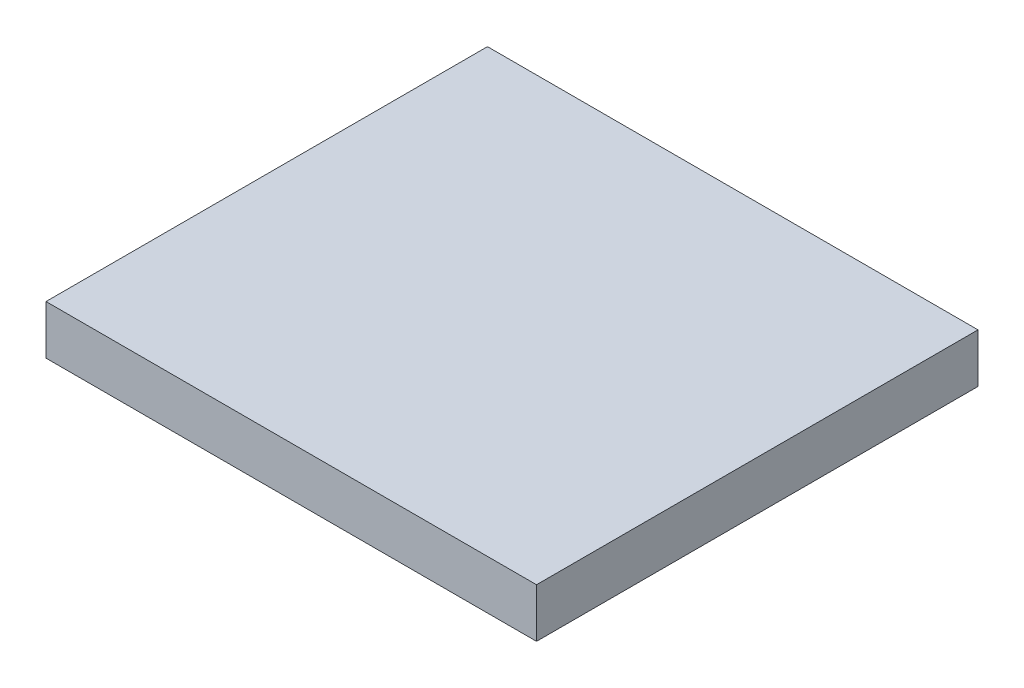
SolidWorks part; units mm, degrees
ref_plane "Front Plane" through (0, 0, 0) normal (0, 0, 1) x (1, 0, 0)
ref_plane "Top Plane" through (0, 0, 0) normal (0, 1, 0) x (1, 0, 0)
ref_plane "Right Plane" through (0, 0, 0) normal (1, 0, 0) x (0, 0, -1)
sketch "Sketch1" plane through (0, 0, 0) normal (0, 1, 0) x (1, 0, 0)
  line L1 (254, -228.6) -> (-254, -228.6)
  line L2 (254, -228.6) -> (254, 228.6)
  line L3 (254, 228.6) -> (-254, 228.6)
  line L4 (-254, -228.6) -> (-254, 228.6)
  line L5 (254, -228.6) -> (-254, 228.6) construction
  line L6 (254, 228.6) -> (-254, -228.6) construction
  point P0 (0, 0)
  dimension "D1" = 508
  dimension "D2" = 457.2
extrude "Boss-Extrude1" add sketch "Sketch1" along normal blind 50.8
